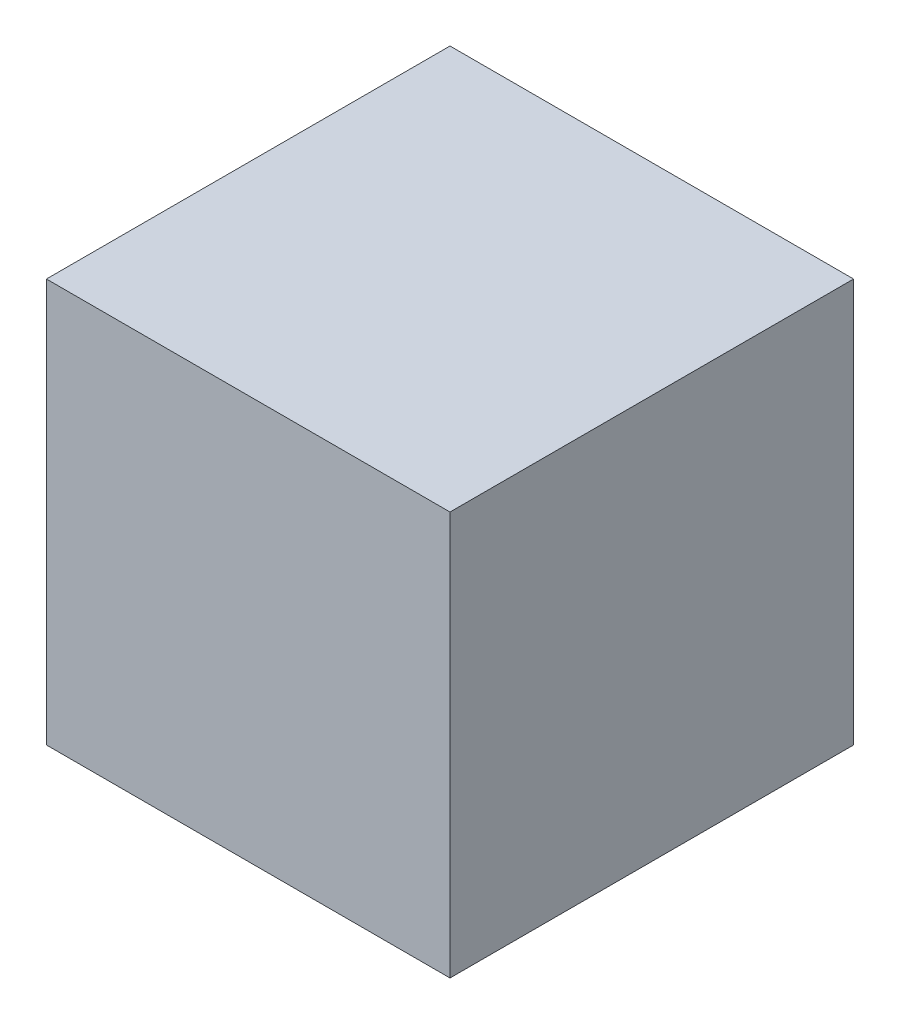
SolidWorks part; units mm, degrees
ref_plane "正面" through (0, 0, 0) normal (0, 0, 1) x (1, 0, 0)
ref_plane "平面" through (0, 0, 0) normal (0, 1, 0) x (1, 0, 0)
ref_plane "右側面" through (0, 0, 0) normal (1, 0, 0) x (0, 0, -1)
sketch "ｽｹｯﾁ2" plane through (0, 0, 0) normal (0, 0, 1) x (1, 0, 0)
  line L1 (0, 0) -> (10, 0)
  line L2 (0, 0) -> (0, 10)
  line L3 (0, 10) -> (10, 10)
  line L4 (10, 0) -> (10, 10)
  dimension "D1" = 10
  dimension "D2" = 10
extrude "ﾎﾞｽ - 押し出し1" add sketch "ｽｹｯﾁ2" along normal blind 10
equation "\"x\"= 10"
equation "\"y\"= 10"
equation "\"z\"= 10"
equation "\"D1@ｽｹｯﾁ2\"=\"x\""
equation "\"D2@ｽｹｯﾁ2\"=\"y\""
equation "\"D1@ﾎﾞｽ - 押し出し1\"=\"z\""
